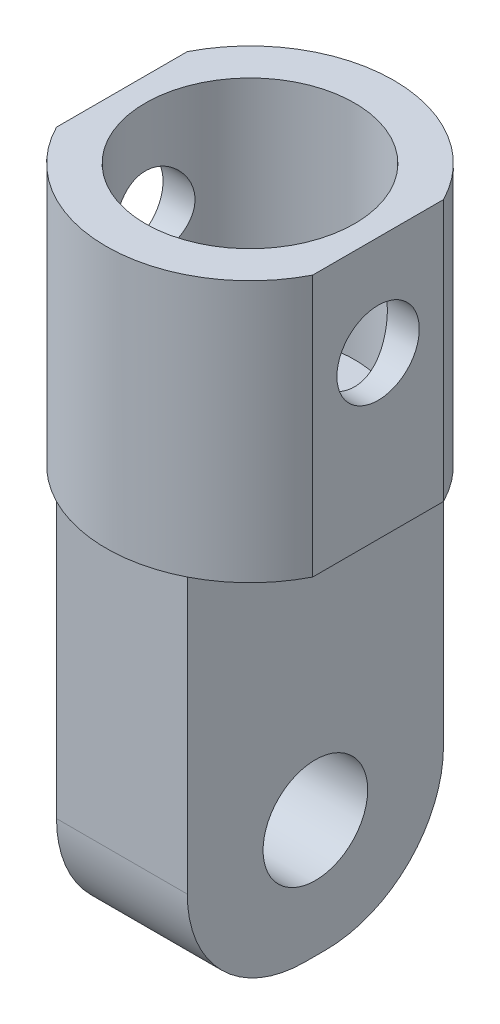
SolidWorks part; units mm, degrees
ref_plane "Спереди" through (0, 0, 0) normal (0, 0, 1) x (1, 0, 0)
ref_plane "Сверху" through (0, 0, 0) normal (0, 1, 0) x (1, 0, 0)
ref_plane "Справа" through (0, 0, 0) normal (1, 0, 0) x (0, 0, -1)
sketch "Sketch1" plane through (0, 0, 0) normal (0, 1, 0) x (1, 0, 0)
  circle A0 centre (0, 0) radius 11
  dimension "D1" = 22
extrude "Boss-Extrude1" add sketch "Sketch1" along normal blind 20
sketch "Sketch2" plane through (0, 20, 0) normal (0, 1, 0) x (1, 0, 0)
  circle A0 centre (0, 0) radius 8
  dimension "D1" = 16
extrude "Cut-Extrude1" cut sketch "Sketch2" against normal blind 17
sketch "Sketch3" plane through (0, 0, 0) normal (0, -1, 0) x (1, 0, 0)
  line L1 (-5, 9.798) -> (5, 9.798)
  line L2 (-5, 9.798) -> (-5, -9.798)
  line L3 (-5, -9.798) -> (5, -9.798)
  line L4 (5, 9.798) -> (5, -9.798)
  line L5 (-5, 9.798) -> (5, -9.798) construction
  line L6 (-5, -9.798) -> (5, 9.798) construction
  circle A0 centre (0, 0) radius 11 construction
  point P0 (0, 0)
  dimension "D1" = 10
extrude "Boss-Extrude2" add sketch "Sketch3" along normal blind 30
sketch "Sketch4" plane through (5, 0, 0) normal (1, 0, 0) x (0, 0, -1)
  line L0 (0, -30) -> (0, 0) construction
  line L1 (9.798, -30) -> (-9.798, -30) construction
  line L2 (9.798, 0) -> (-9.798, 0) construction
  circle A0 centre (0, -21) radius 4
  dimension "D1" = 8
  dimension "D2" = 9
extrude "Cut-Extrude2" cut sketch "Sketch4" against normal through all
fillet "Fillet1" radius 9 2 edges at (0, -30, 9.798) (0, -30, -9.798)
sketch "Sketch5" plane through (0, 20, 0) normal (0, 1, 0) x (1, 0, 0)
  line L0 (-9.798, 5) -> (-9.798, -5)
  line L1 (9.798, -5) -> (9.798, 5)
  circle A0 centre (0, 0) radius 11 construction
  arc A1 (-9.798, -5) -> (-9.798, 5) centre (0, 0) cw
  arc A2 (9.798, 5) -> (9.798, -5) centre (0, 0) cw
  dimension "D1" = 10
extrude "Cut-Extrude3" cut sketch "Sketch5" against normal through all
sketch "Sketch6" plane through (-9.798, 0, 0) normal (-1, 0, 0) x (0, 0, 1)
  line L0 (0, 0) -> (0, 20) construction
  line L1 (5, 0) -> (-5, 0) construction
  line L2 (5, 20) -> (-5, 20) construction
  circle A0 centre (0, 12.35) radius 3.15
  point P8 (0, 15.5)
  dimension "D1" = 6.3
  dimension "D2" = 4.5
extrude "Cut-Extrude4" cut sketch "Sketch6" against normal through all
